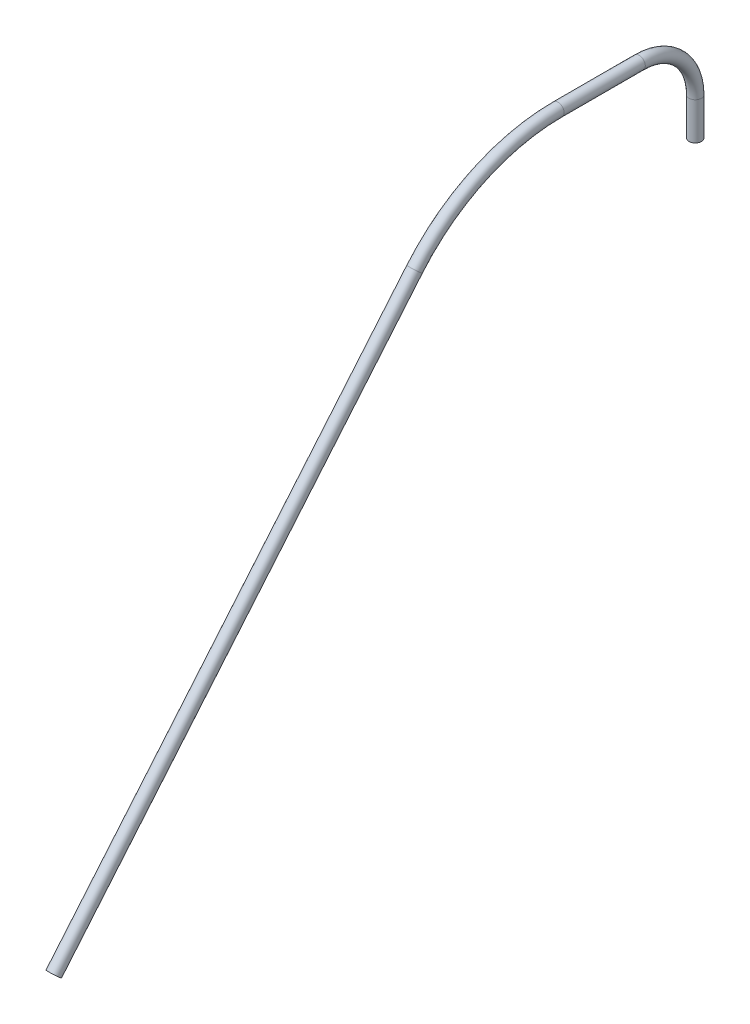
SolidWorks part; units mm, degrees
ref_plane "Front Plane" through (0, 0, 0) normal (0, 0, 1) x (1, 0, 0)
ref_plane "Top Plane" through (0, 0, 0) normal (0, 1, 0) x (1, 0, 0)
ref_plane "Right Plane" through (0, 0, 0) normal (1, 0, 0) x (0, 0, -1)
sketch "Sketch1" plane through (0, 0, 0) normal (0, 1, 0) x (1, 0, 0)
  circle A0 centre (0, 0) radius 3.3
  dimension "D1" = 6.6
sketch "Sketch2" plane through (0, 0, 0) normal (1, 0, 0) x (0, 0, -1)
  line L0 (0, 0) -> (0, 20)
  line L1 (-30, 50) -> (-73.3956, 50)
  line L2 (-150, 14.2788) -> (-342.8363, -215.5346)
  line L3 (0, 0) -> (-20.7759, 0) construction
  line L4 (-342.8363, -215.5346) -> (-319.0582, -215.5346) construction
  arc A0 (-150, 14.2788) -> (-73.3956, 50) centre (-73.3956, -50) cw
  arc A1 (0, 20) -> (-30, 50) centre (-30, 20) ccw
  point P11 (0, 50)
  dimension "D4" = 100
  dimension "D7" = 30
  dimension "D1" = 50
  dimension "D2" = 90
  dimension "D3" = 50
  dimension "D5" = 300
  dimension "D6" = 150
sweep "Sweep1" add profiles "Sketch1" path "Sketch2"
